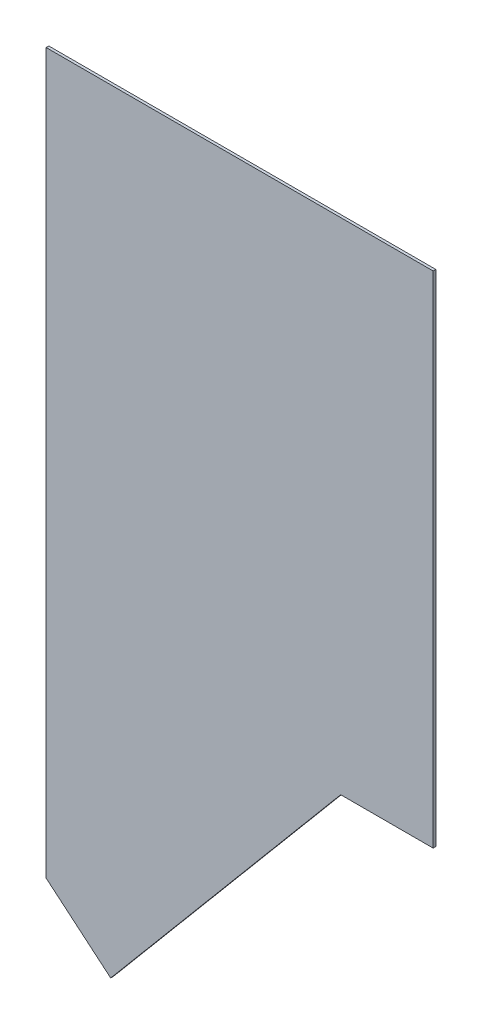
SolidWorks part; units mm, degrees
material "Acrylic (Medium-high impact)"
ref_plane "Front Plane" through (0, 0, 0) normal (0, 0, 1) x (1, 0, 0)
ref_plane "Top Plane" through (0, 0, 0) normal (0, 1, 0) x (1, 0, 0)
ref_plane "Right Plane" through (0, 0, 0) normal (1, 0, 0) x (0, 0, -1)
sketch "Sketch1" plane through (0, 0, 0) normal (0, 0, 1) x (1, 0, 0)
  line L1 (-50.8, 0) -> (254, 0)
  line L2 (-50.8, 0) -> (-50.8, -609.6)
  line L3 (-50.8, -609.6) -> (254, -609.6)
  line L4 (254, 0) -> (254, -609.6)
extrude "Boss-Extrude1" add sketch "Sketch1" along normal blind 2.1082
sketch "Sketch2" plane through (0, 0, 2.1082) normal (0, 0, 1) x (1, 0, 0)
  line L0 (-50.8, -609.6) -> (-50.8, -566.6184)
  line L1 (-50.8, 0) -> (-50.8, -609.6) construction
  line L2 (-50.8, -566.6184) -> (0, -609.305)
  line L3 (0, -609.305) -> (156.4912, -423.0696)
  line L4 (156.4912, -423.0696) -> (181.1702, -393.7)
  line L5 (-50.8, -393.7) -> (254, -393.7) construction
  line L6 (181.1702, -393.7) -> (254, -393.7)
  line L7 (254, -393.7) -> (254, -609.6)
  line L8 (254, -609.6) -> (254, 0) construction
  line L9 (-50.8, -609.6) -> (254, -609.6) construction
  line L10 (254, -609.6) -> (-50.8, -609.6)
extrude "Cut-Extrude1" cut sketch "Sketch2" against normal blind 2.1082
